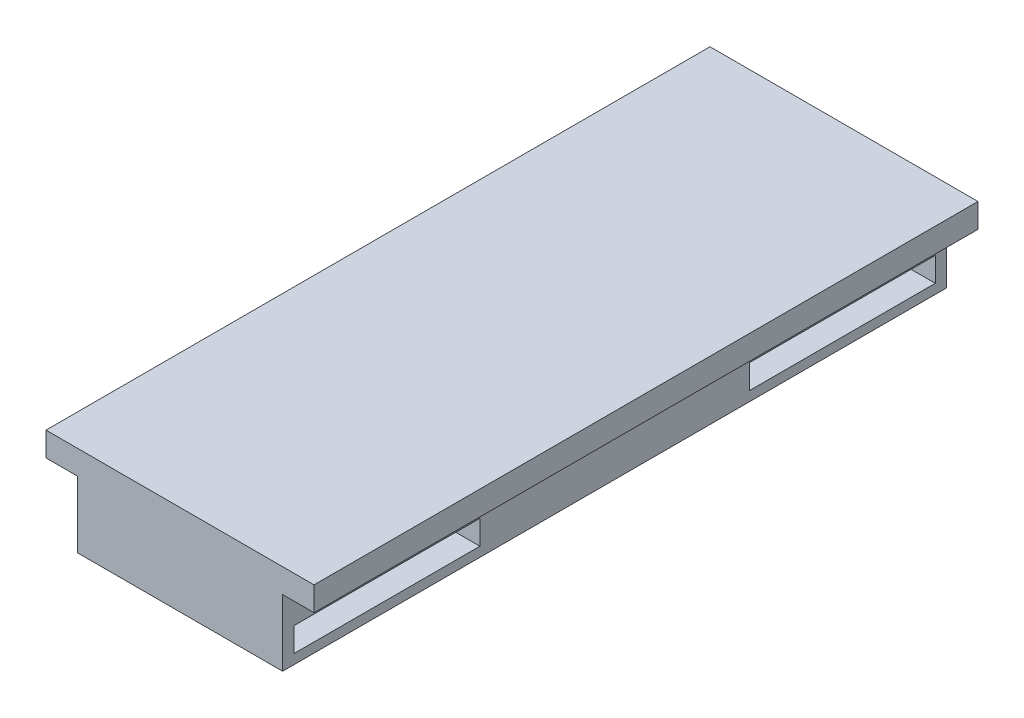
SolidWorks part; units mm, degrees
ref_plane "Front Plane" through (0, 0, 0) normal (0, 0, 1) x (1, 0, 0)
ref_plane "Top Plane" through (0, 0, 0) normal (0, 1, 0) x (1, 0, 0)
ref_plane "Right Plane" through (0, 0, 0) normal (1, 0, 0) x (0, 0, -1)
sketch "Sketch2" plane through (0, 0, 0) normal (0, 0, 1) x (1, 0, 0)
  line L0 (2.6, -2.2808) -> (19.6, -2.2808)
  line L1 (2.6, -2.2808) -> (2.6, 3.2192)
  line L2 (19.6, -2.2808) -> (19.6, 3.2192)
  line L3 (2.6, 3.2192) -> (0, 3.2192)
  line L4 (0, 3.2192) -> (0, 5.2192)
  line L5 (22.2, 5.2192) -> (22.2, 3.2192)
  line L6 (22.2, 3.2192) -> (19.6, 3.2192)
  line L7 (0, 5.2192) -> (22.2, 5.2192)
  line L8 (0, -55) -> (0, 55) construction
  dimension "D1" = 2
  dimension "D2" = 2
  dimension "D3" = 17
  dimension "D4" = 5.5
  dimension "D5" = 2.6
  dimension "D6" = 2.6
extrude "Boss-Extrude1" add sketch "Sketch2" against normal blind 55
sketch "Sketch3" plane through (0, -2.2808, 0) normal (0, -1, 0) x (1, 0, 0)
  line L0 (11.1, -46.36) -> (11.1, -54.832) construction
  line L5 (2.6, -27.5) -> (11.1, -27.5) construction
  line L6 (11.1, -8.64) -> (11.1, -46.36) construction
  line L11 (55, 0) -> (-55, 0) construction
  line L12 (2.6, -55) -> (19.6, -55) construction
  line L14 (19.6, -55) -> (19.6, 0) construction
  line L15 (2.6, -55) -> (2.6, 0) construction
  circle A2 centre (11.1, -8.64) radius 7.7
  circle A3 centre (11.1, -46.36) radius 7.7
  point P14 (11.1, -27.5)
  dimension "D1" = 15.4
  dimension "D2" = 15.4
  dimension "D3" = 8.64
  dimension "D4" = 46.36
  dimension "D5" = 8.472
  dimension "D6" = 8.64
  dimension "D7" = 8.5
  dimension "D8" = 8.5
extrude "Cut-Extrude1" cut sketch "Sketch3" against normal blind 2.8
sketch "Sketch4" plane through (0, -2.2808, 0) normal (0, -1, 0) x (1, 0, 0)
  circle A0 centre (11.1, -8.64) radius 7.7
  circle A1 centre (11.1, -46.36) radius 7.7
  circle A2 centre (11.1, -8.64) radius 5.5
  circle A3 centre (11.1, -46.36) radius 5.5
  dimension "D1" = 11
  dimension "D2" = 11
extrude "Boss-Extrude2" add sketch "Sketch4" against normal blind 0.8
sketch "Sketch5" plane through (19.6, 0, 0) normal (1, 0, 0) x (0, 0, -1)
  line L1 (0.94, 0.5192) -> (16.34, 0.5192)
  line L2 (0.94, 0.5192) -> (0.94, -1.4808)
  line L3 (0.94, -1.4808) -> (16.34, -1.4808)
  line L4 (16.34, 0.5192) -> (16.34, -1.4808)
  line L5 (38.66, 0.5192) -> (54.06, 0.5192)
  line L6 (38.66, 0.5192) -> (38.66, -1.4808)
  line L7 (38.66, -1.4808) -> (54.06, -1.4808)
  line L8 (54.06, 0.5192) -> (54.06, -1.4808)
  line L10 (55, -2.2808) -> (0, -2.2808) construction
  line L11 (0.94, 0.5192) -> (0.94, -1.4808) construction
  line L12 (54.06, -1.4808) -> (54.06, 0.5192) construction
  dimension "D1" = 0
  dimension "D2" = 0
  dimension "D3" = 15.4
  dimension "D4" = 15.4
  dimension "D5" = 0.8
  dimension "D6" = 0.8
  dimension "D7" = 2
  dimension "D8" = 2
extrude "Cut-Extrude2" cut sketch "Sketch5" against normal blind 8.5
